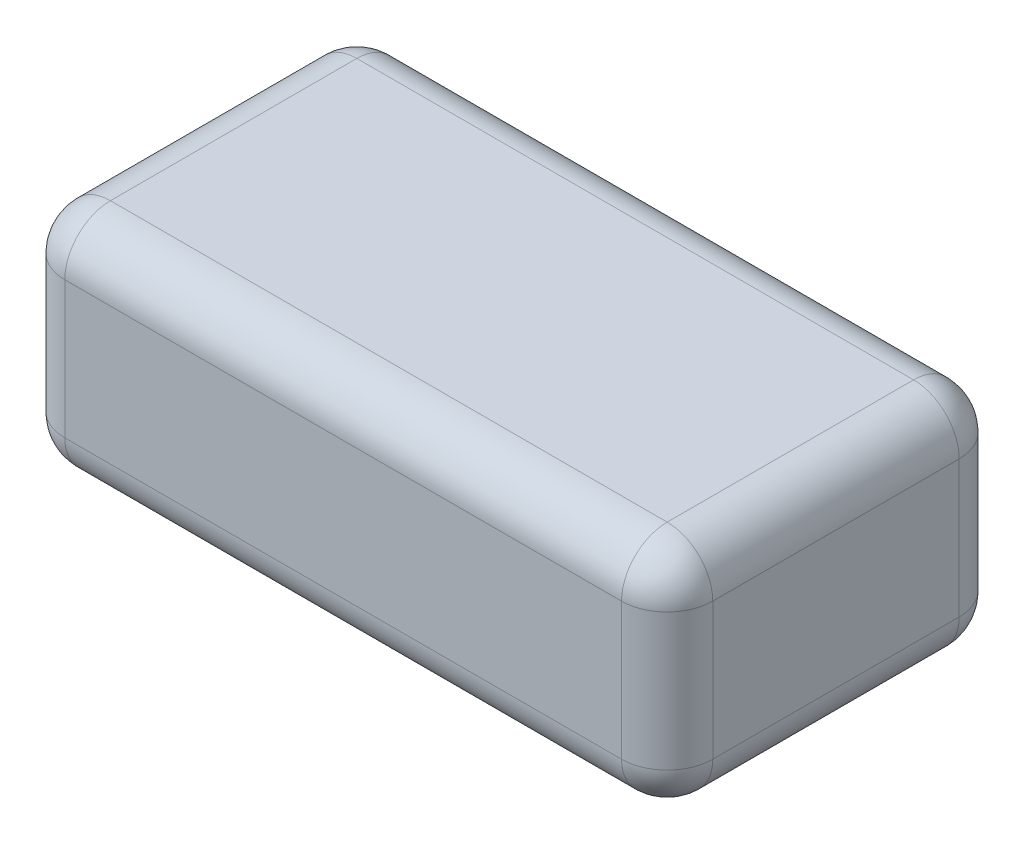
SolidWorks part; units mm, degrees
ref_plane "Alzado" through (0, 0, 0) normal (0, 0, 1) x (1, 0, 0)
ref_plane "Planta" through (0, 0, 0) normal (0, 1, 0) x (1, 0, 0)
ref_plane "Vista lateral" through (0, 0, 0) normal (1, 0, 0) x (0, 0, -1)
sketch "Croquis1" plane through (0, 0, 0) normal (0, 1, 0) x (1, 0, 0)
  line L1 (-35.5, -18.5) -> (35.5, -18.5)
  line L2 (-35.5, -18.5) -> (-35.5, 18.5)
  line L3 (-35.5, 18.5) -> (35.5, 18.5)
  line L4 (35.5, -18.5) -> (35.5, 18.5)
  line L5 (-35.5, -18.5) -> (35.5, 18.5) construction
  line L6 (-35.5, 18.5) -> (35.5, -18.5) construction
  point P0 (0, 0)
  dimension "D1" = 71
  dimension "D2" = 37
extrude "Saliente-Extruir1" add sketch "Croquis1" along normal blind 25
fillet "Redondeo3" radius 5 12 edges at (0, 0, 18.5) (35.5, 12.5, 18.5) (35.5, 0, 0) (0, 25, 18.5) (35.5, 25, 0) (-35.5, 25, 0) (-35.5, 12.5, 18.5) (-35.5, 0, 0) (35.5, 12.5, -18.5) (0, 25, -18.5) (-35.5, 12.5, -18.5) (0, 0, -18.5)
